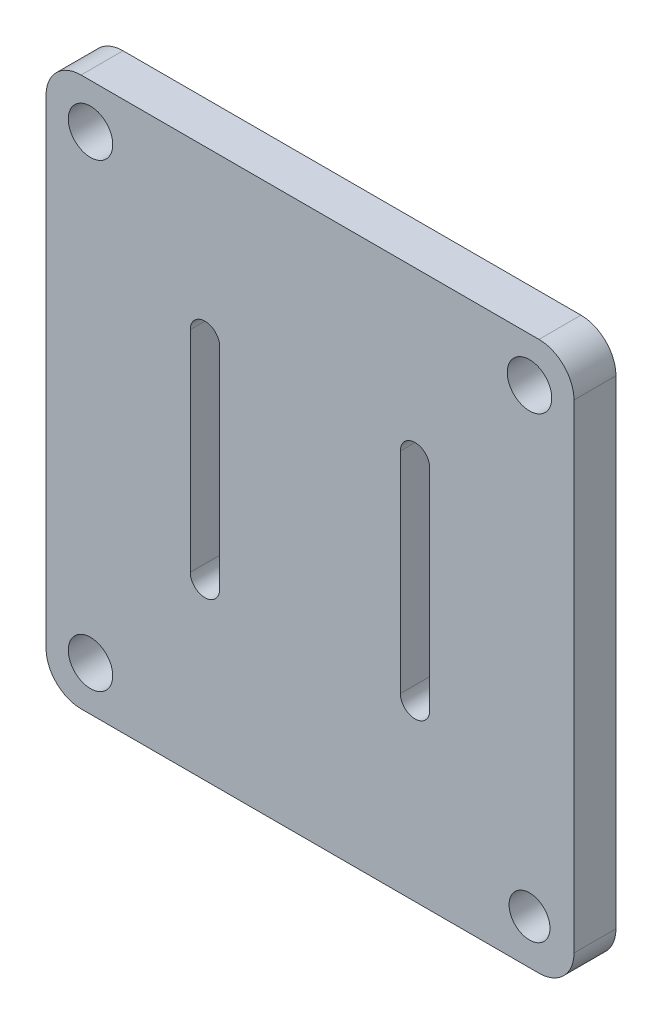
SolidWorks part; units mm, degrees
ref_plane "Front Plane" through (0, 0, 0) normal (0, 0, 1) x (1, 0, 0)
ref_plane "Top Plane" through (0, 0, 0) normal (0, 1, 0) x (1, 0, 0)
ref_plane "Right Plane" through (0, 0, 0) normal (1, 0, 0) x (0, 0, -1)
sketch "Sketch1" plane through (0, 0, 0) normal (0, 0, 1) x (-1, 0, 0)
  line L0 (589.3171, -630.6689) -> (589.3171, -660.6689)
  line L1 (591.4139, -630.6689) -> (591.4139, -660.6689)
  line L2 (587.2203, -630.6689) -> (587.2203, -660.6689)
  line L3 (619.3171, -630.6689) -> (619.3171, -660.6689)
  line L4 (621.4192, -630.6689) -> (621.4192, -660.6689)
  line L5 (617.2149, -630.6689) -> (617.2149, -660.6689)
  line L6 (579.3171, -661.6689) -> (589.3171, -671.6689) construction
  line L7 (579.3171, -618.6689) -> (629.3171, -618.6689) construction
  line L8 (579.3171, -618.6689) -> (579.3171, -661.6689) construction
  line L9 (589.3171, -671.6689) -> (619.3171, -671.6689) construction
  line L10 (629.3171, -618.6689) -> (629.3171, -661.6689) construction
  line L11 (619.3171, -671.6689) -> (629.3171, -661.6689) construction
  line L12 (579.3171, -618.6689) -> (566.6171, -618.6689) construction
  line L13 (579.3171, -618.6689) -> (579.3171, -605.9689) construction
  line L14 (629.3171, -661.6689) -> (642.0171, -661.6689) construction
  line L15 (619.3171, -671.6689) -> (619.3171, -684.3689) construction
  line L16 (642.0171, -679.3689) -> (642.0171, -610.9689)
  line L17 (637.0171, -605.9689) -> (571.6171, -605.9689)
  line L18 (566.6171, -610.9689) -> (566.6171, -679.3689)
  line L19 (571.6171, -684.3689) -> (637.0171, -684.3689)
  line L20 (642.0171, -684.3689) -> (641.9755, -684.3727)
  line L21 (572.9671, -618.6689) -> (572.9671, -612.3189) construction
  line L22 (572.9671, -612.3189) -> (635.6671, -612.3189) construction
  line L23 (635.6671, -612.3189) -> (635.6671, -678.0189) construction
  line L24 (635.6671, -678.0189) -> (572.9671, -678.0189) construction
  arc A0 (591.4139, -630.6689) -> (587.2203, -630.6689) centre (589.3171, -630.6689) ccw
  arc A1 (587.2203, -660.6689) -> (591.4139, -660.6689) centre (589.3171, -660.6689) ccw
  arc A2 (621.4192, -630.6689) -> (617.2149, -630.6689) centre (619.3171, -630.6689) ccw
  arc A3 (617.2149, -660.6689) -> (621.4192, -660.6689) centre (619.3171, -660.6689) ccw
  circle A4 centre (572.9671, -612.3189) radius 2.921
  circle A5 centre (635.6671, -612.3189) radius 3.175
  circle A6 centre (635.6671, -678.0189) radius 3.175
  circle A7 centre (572.9671, -678.0189) radius 3.175
  arc A8 (571.6171, -605.9689) -> (566.6171, -610.9689) centre (571.6171, -610.9689) ccw
  arc A9 (642.0171, -610.9689) -> (637.0171, -605.9689) centre (637.0171, -610.9689) ccw
  arc A10 (637.0171, -684.3689) -> (642.0171, -679.3689) centre (637.0171, -679.3689) ccw
  arc A11 (566.6171, -679.3689) -> (571.6171, -684.3689) centre (571.6171, -679.3689) ccw
  point P4 (589.3171, -645.6689)
  point P9 (619.3171, -645.6689)
  point P19 (629.3171, -671.6689)
  point P20 (579.3171, -671.6689)
  dimension "D1" = 5
  dimension "D2" = 5
  dimension "D5" = 5
  dimension "D6" = 5
extrude "Boss-Extrude1" add sketch "Sketch1" along normal blind 5.9944 contours L18 A11 L19 A10 L16 A9 L17 A8 A1 L2 A0 L1 A3 L5 A2 L4 A4 A5 A6 A7
